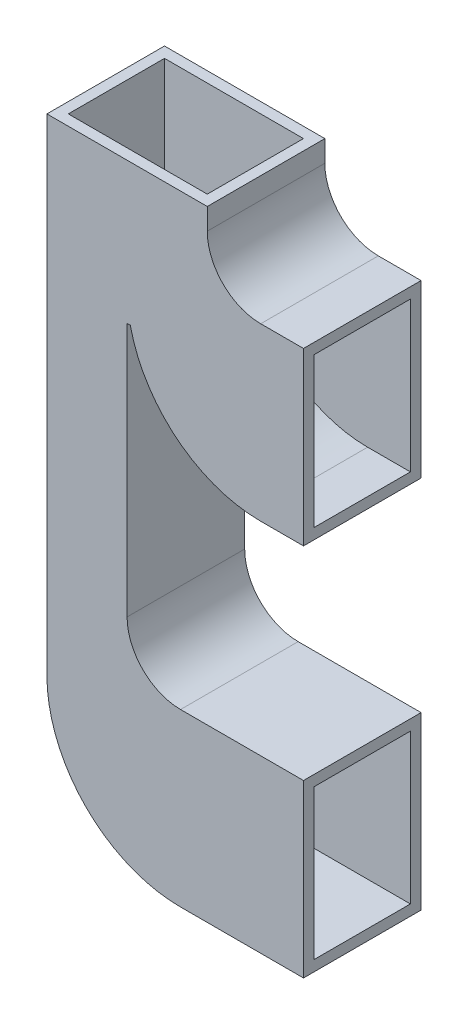
SolidWorks part; units mm, degrees
ref_plane "Plano frontal" through (0, 0, 0) normal (0, 0, 1) x (1, 0, 0)
ref_plane "Plano superior" through (0, 0, 0) normal (0, 1, 0) x (1, 0, 0)
ref_plane "Plano direito" through (0, 0, 0) normal (1, 0, 0) x (0, 0, -1)
sketch "Esboço1" plane through (0, 0, 0) normal (0, 0, 1) x (1, 0, 0)
  line L0 (0, 45.5) -> (0, 0)
  line L1 (12.5, -12.5) -> (24, -12.5)
  line L2 (24, -12.5) -> (24, 3.5)
  line L3 (24, 3.5) -> (12.5, 3.5)
  line L4 (7.5, 8.5) -> (7.5, 32.2779)
  line L5 (20, 22.5) -> (24, 22.5)
  line L6 (12.5, -12.5) -> (12.5, -2.2893) construction
  line L7 (24, 22.5) -> (24, 38.5)
  line L8 (24, 38.5) -> (20, 38.5)
  line L10 (15, 45.5) -> (0, 45.5)
  line L11 (15, 43.5) -> (15, 45.5)
  line L12 (7.8, 32.2779) -> (7.5, 32.2779)
  arc A0 (0, 0) -> (12.5, -12.5) centre (12.5, 0) ccw
  arc A1 (12.5, 3.5) -> (7.5, 8.5) centre (12.5, 8.5) cw
  arc A2 (7.8, 32.2779) -> (20, 22.5) centre (20, 35) ccw
  arc A3 (20, 38.5) -> (15, 43.5) centre (20, 43.5) cw
  point P11 (8.5282, 29.6946)
  point P23 (7.5, 45.5)
  dimension "D6" = 5
  dimension "D1" = 16
  dimension "D2" = 4
  dimension "D3" = 15
  dimension "D4" = 35
  dimension "D5" = 7
  dimension "D7" = 0.3
extrude "Ressalto-extrusão1" add sketch "Esboço1" along normal blind 11
shell "Casca2" thickness 1
